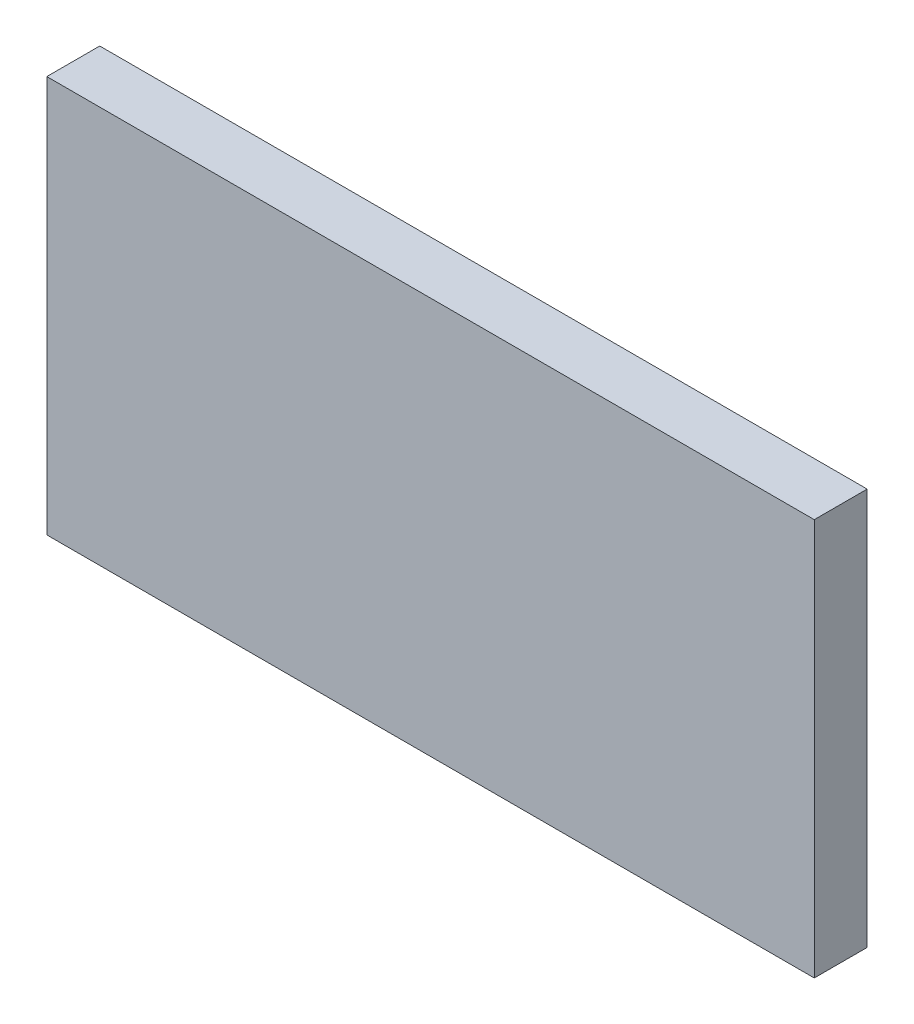
SolidWorks part; units mm, degrees
ref_plane "Ön Düzlem" through (0, 0, 0) normal (0, 0, 1) x (1, 0, 0)
ref_plane "Üst Düzlem" through (0, 0, 0) normal (0, 1, 0) x (1, 0, 0)
ref_plane "Sağ Düzlem" through (0, 0, 0) normal (1, 0, 0) x (0, 0, -1)
sketch "Sketch1" plane through (0, 0, 0) normal (0, 0, 1) x (1, 0, 0)
  line L1 (-18.6495, 23.3789) -> (39.3505, 23.3789)
  line L2 (-18.6495, 23.3789) -> (-18.6495, -6.6211)
  line L3 (-18.6495, -6.6211) -> (39.3505, -6.6211)
  line L4 (39.3505, 23.3789) -> (39.3505, -6.6211)
  dimension "D1" = 58
  dimension "D2" = 30
extrude "Boss-Extrude1" add sketch "Sketch1" along normal blind 4
